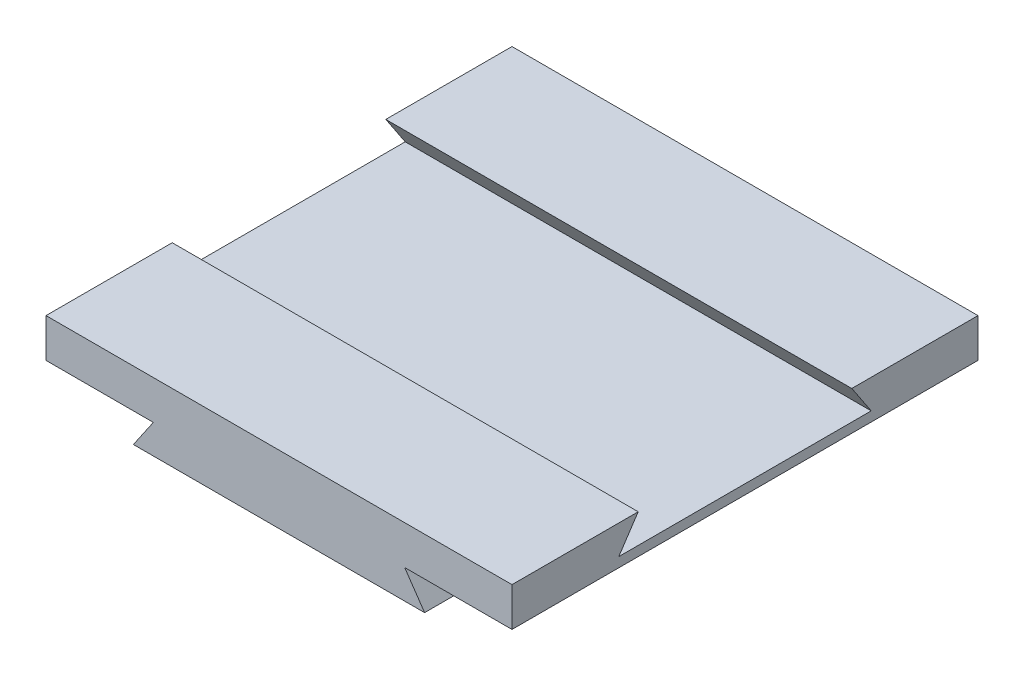
SolidWorks part; units mm, degrees
ref_plane "Спереди" through (0, 0, 0) normal (0, 0, 1) x (1, 0, 0)
ref_plane "Сверху" through (0, 0, 0) normal (0, 1, 0) x (1, 0, 0)
ref_plane "Справа" through (0, 0, 0) normal (1, 0, 0) x (0, 0, -1)
sketch "Эскиз1" plane through (0, 0, 0) normal (0, 0, 1) x (1, 0, 0)
  line L0 (0, 0) -> (75, 0)
  line L1 (75, 0) -> (64.72, 15)
  line L2 (64.72, 15) -> (120, 15)
  line L3 (120, 15) -> (120, 35)
  line L4 (120, 35) -> (0, 35)
  line L5 (0, 56.4782) -> (0, 0) construction
  line L6 (-120, 35) -> (0, 35)
  line L7 (-120, 15) -> (-120, 35)
  line L8 (-64.72, 15) -> (-120, 15)
  line L9 (-75, 0) -> (-64.72, 15)
  line L10 (0, 0) -> (-75, 0)
  line L11 (-75, 0) -> (75, 0) construction
  dimension "D1" = 20
  dimension "D2" = 75
  dimension "D3" = 120
extrude "Бобышка-Вытянуть1" add sketch "Эскиз1" along normal blind 240
sketch "Эскиз2" plane through (-120, 0, 0) normal (-1, 0, 0) x (0, 0, 1)
  line L0 (120, 35) -> (120, -3.231) construction
  line L1 (240, 35) -> (0, 35) construction
  line L6 (65, 35) -> (175, 35)
  line L7 (175, 35) -> (185, 20)
  line L8 (185, 20) -> (55, 20)
  line L9 (65, 35) -> (55, 20)
  point P9 (120, 20)
  dimension "D1" = 65
  dimension "D2" = 15
  dimension "D3" = 55
extrude "Вырез-Вытянуть1" cut sketch "Эскиз2" against normal through all
